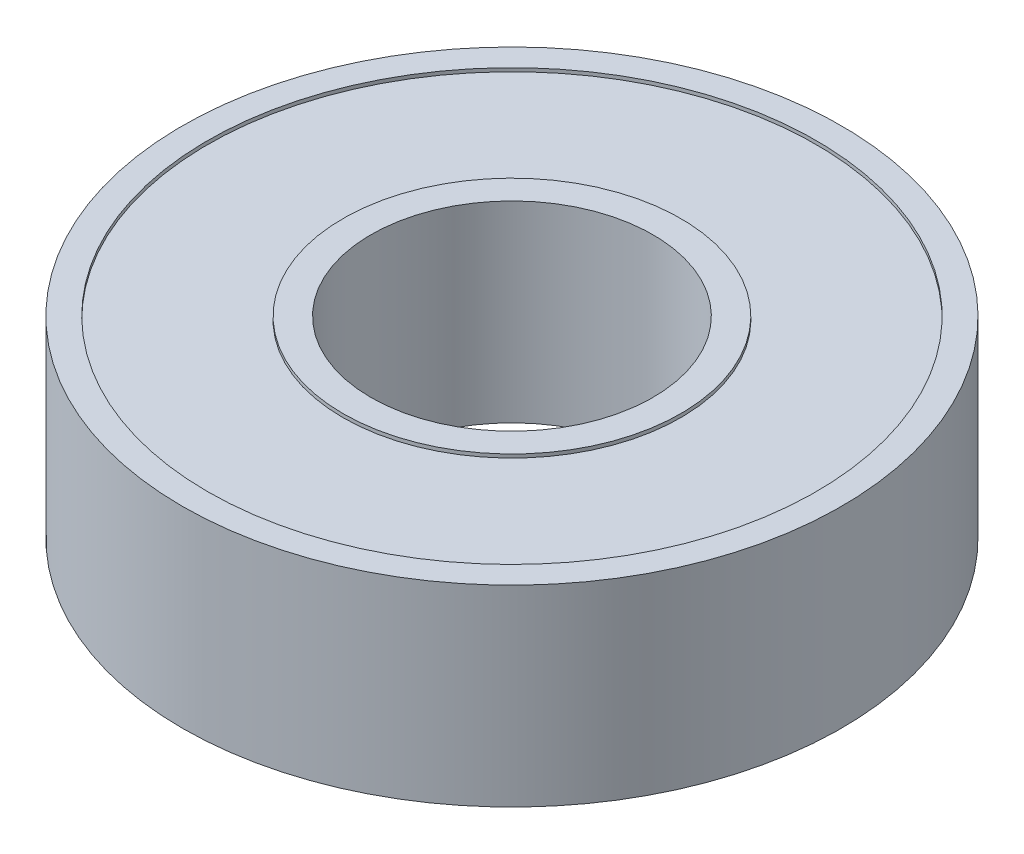
SolidWorks part; units mm, degrees
ref_plane "Alzado" through (0, 0, 0) normal (0, 0, 1) x (1, 0, 0)
ref_plane "Planta" through (0, 0, 0) normal (0, 1, 0) x (1, 0, 0)
ref_plane "Vista lateral" through (0, 0, 0) normal (1, 0, 0) x (0, 0, -1)
sketch "Croquis1" plane through (0, 0, 0) normal (0, 1, 0) x (1, 0, 0)
  circle A0 centre (0, 0) radius 13.975
  dimension "D1" = 27.95
extrude "Saliente-Extruir1" add sketch "Croquis1" along normal blind 8
sketch "Croquis2" plane through (0, 8, 0) normal (0, 1, 0) x (1, 0, 0)
  circle A0 centre (0, 0) radius 5.98
  dimension "D1" = 11.96
extrude "Cortar-Extruir1" cut sketch "Croquis2" against normal blind 8
sketch "Croquis3" plane through (0, 8, 0) normal (0, 1, 0) x (1, 0, 0)
  circle A0 centre (0, 0) radius 7.1633
  circle A1 centre (0, 0) radius 5.98
extrude "Saliente-Extruir3" add sketch "Croquis3" along normal blind 0.15
sketch "Croquis4" plane through (0, 0, 0) normal (0, 1, 0) x (1, 0, 0)
  circle A0 centre (0, 0) radius 12.8998
  circle A1 centre (0, 0) radius 13.975
extrude "Saliente-Extruir4" add sketch "Croquis4" along normal blind 8.15
